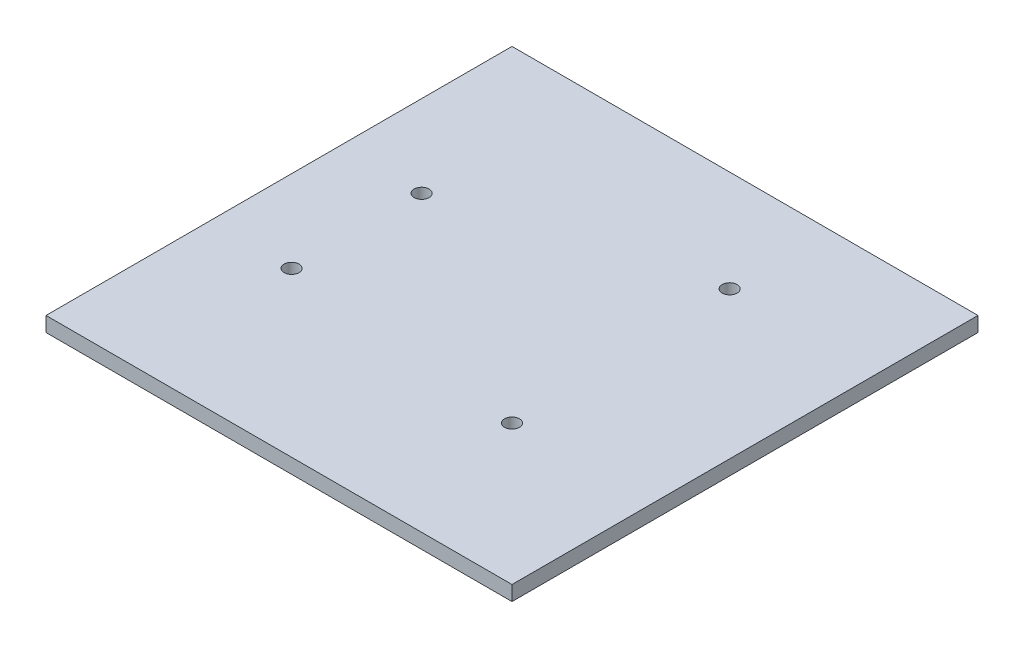
SolidWorks part; units mm, degrees
ref_plane "Front Plane" through (0, 0, 0) normal (0, 0, 1) x (1, 0, 0)
ref_plane "Top Plane" through (0, 0, 0) normal (0, 1, 0) x (1, 0, 0)
ref_plane "Right Plane" through (0, 0, 0) normal (1, 0, 0) x (0, 0, -1)
sketch "Sketch1" plane through (0, 0, 0) normal (0, 1, 0) x (1, 0, 0)
  line L1 (50, 50) -> (-50, 50)
  line L2 (50, 50) -> (50, -50)
  line L3 (50, -50) -> (-50, -50)
  line L4 (-50, 50) -> (-50, -50)
  line L5 (50, 50) -> (-50, -50) construction
  line L6 (50, -50) -> (-50, 50) construction
  point P0 (0, 0)
  dimension "D1" = 100
  dimension "D2" = 100
extrude "Boss-Extrude1" add sketch "Sketch1" along normal blind 3.18 contours L2 L1 L4 L3
sketch "Sketch2" plane through (0, 3.18, 0) normal (0, 1, 0) x (1, 0, 0)
  line L0 (50, -50) -> (50, 50) construction
  line L1 (-50, -50) -> (50, -50) construction
  line L2 (20, -20) -> (20, 28.3) construction
  circle A0 centre (-32.4, 13) radius 1.6
  circle A1 centre (-32.4, -14.9) radius 1.6
  circle A2 centre (18.4, 28.3) radius 1.6
  circle A3 centre (20, -20) radius 1.6
  dimension "D1" = 3.2
  dimension "D2" = 50.8
  dimension "D3" = 27.9
  dimension "D7" = 5.1
  dimension "D4" = 48.3
  dimension "D5" = 30
  dimension "D6" = 30
extrude "Cut-Extrude1" cut sketch "Sketch2" against normal through all
sketch "Sketch3" [suppressed] plane through (0, 0, 0) normal (0, -1, 0) x (1, 0, 0)
  line L0 (0, -1.2222) -> (0, -24.0948) construction
  line L1 (-13.75, -6.5) -> (13.75, -6.5) construction
  line L2 (50, 30) -> (-50, 30) construction
  circle A0 centre (-13.75, -6.5) radius 2
  circle A1 centre (13.75, -6.5) radius 2
  circle A2 centre (0, 15) radius 2
  dimension "D1" = 4
  dimension "D2" = 27.5
  dimension "D3" = 15
  dimension "D4" = 21.5
extrude "Cut-Extrude2" [suppressed] cut sketch "Sketch3" against normal blind 10
ref_plane "Plane1" [suppressed] through (-50, 66.36, -50) normal (0, 0, 1) x (1, 0, 0)
sketch "Sketch5" [suppressed] plane through (0, 0, 0) normal (0, -1, 0) x (1, 0, 0)
  line L0 (0, 0) -> (38.0998, 0) construction
  line L1 (29.5493, -10.8537) -> (29.5493, 18.3981) construction
  line L3 (-35.4792, 12.1463) -> (-22.9792, 12.1463)
  line L4 (-35.4792, 12.1463) -> (-35.4792, -10.8537)
  line L5 (-35.4792, -10.8537) -> (-22.9792, -10.8537)
  line L6 (-22.9792, 12.1463) -> (-22.9792, -10.8537)
  line L7 (-35.4792, 12.1463) -> (-22.9792, -10.8537) construction
  line L8 (-35.4792, -10.8537) -> (-22.9792, 12.1463) construction
  line L9 (-29.2292, 12.1463) -> (-29.2292, -10.8537) construction
  circle A0 centre (29.5493, -18.3981) radius 3.81
  circle A1 centre (29.5493, 18.3981) radius 3.81
  circle A2 centre (-28.9792, 14.1463) radius 1
  circle A3 centre (-28.9792, -12.8537) radius 1
  point P9 (-29.2292, 0.6463)
  dimension "D1" = 7.62
  dimension "D4" = 2
  dimension "D5" = 2
  dimension "D6" = 2
  dimension "D7" = 2
  dimension "D2" = 12.5
  dimension "D3" = 23
  dimension "D8" = 6
  dimension "D9" = 6
extrude "Cut-Extrude3" [suppressed] cut sketch "Sketch5" against normal blind 10
